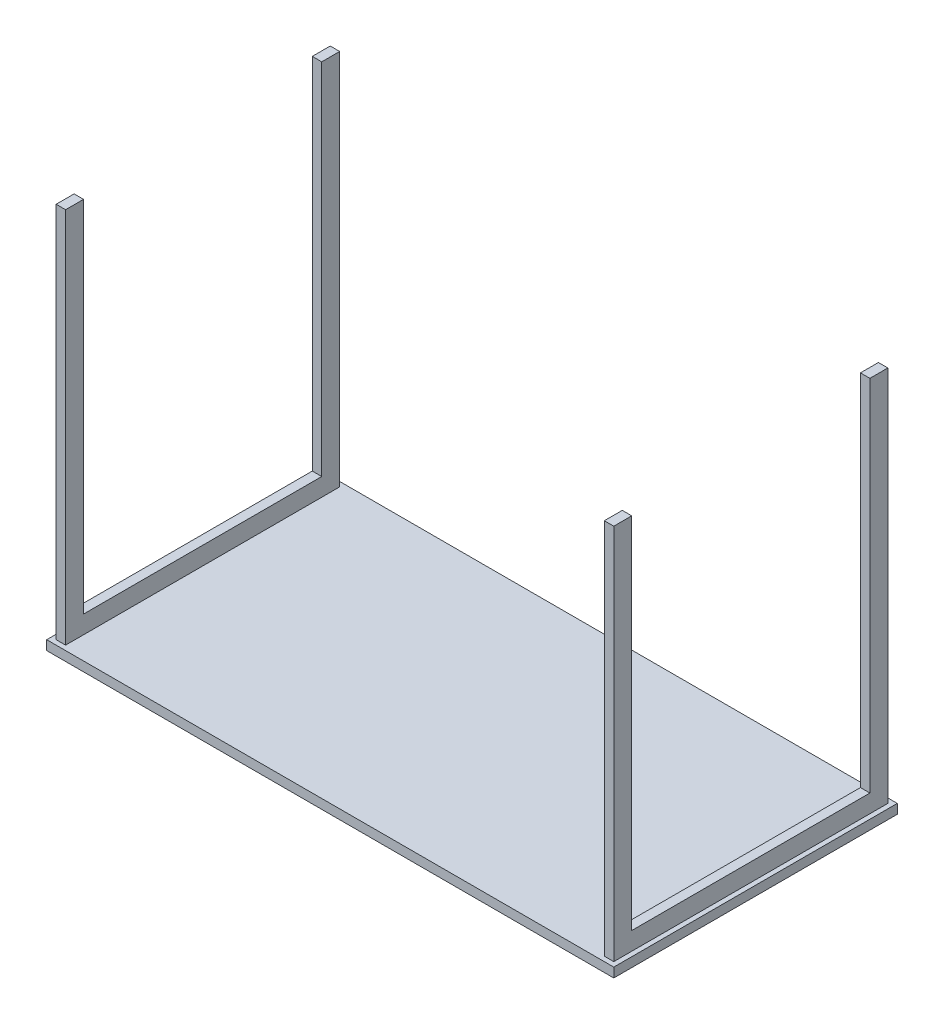
SolidWorks part; units mm, degrees
ref_plane "Front Plane" through (0, 0, 0) normal (0, 0, 1) x (1, 0, 0)
ref_plane "Top Plane" through (0, 0, 0) normal (0, 1, 0) x (1, 0, 0)
ref_plane "Right Plane" through (0, 0, 0) normal (1, 0, 0) x (0, 0, -1)
sketch "Sketch9" plane through (0, 0, 0) normal (0, 1, 0) x (1, 0, 0)
  line L0 (0, 0) -> (0, 600)
  line L1 (0, 0) -> (1200, 0)
  line L2 (0, 600) -> (1200, 600)
  line L3 (1200, 0) -> (1200, 600)
extrude "Boss-Extrude4" add sketch "Sketch9" along normal blind 20
sketch "Sketch10" plane through (0, 20, 0) normal (0, 1, 0) x (1, 0, 0)
  line L0 (10, 590) -> (10, 10)
  line L1 (10, 590) -> (30, 590)
  line L2 (10, 10) -> (30, 10)
  line L3 (30, 590) -> (30, 10)
  line L4 (0, 600) -> (0, 0) construction
  line L6 (1200, 600) -> (0, 600) construction
  line L7 (600, 600) -> (600, 0) construction
  line L8 (0, 0) -> (1200, 0) construction
  line L9 (1170, 590) -> (1170, 10)
  line L10 (1190, 10) -> (1170, 10)
  line L11 (1190, 590) -> (1170, 590)
  line L12 (1190, 590) -> (1190, 10)
  dimension "D1" = 10
  dimension "D2" = 20
  dimension "D3" = 10
  dimension "D4" = 10
extrude "Boss-Extrude6" add sketch "Sketch10" along normal blind 38
sketch "Sketch11" plane through (0, 58, 0) normal (0, 1, 0) x (1, 0, 0)
  line L0 (10, 590) -> (10, 552)
  line L1 (10, 590) -> (30, 590)
  line L2 (10, 552) -> (30, 552)
  line L3 (30, 590) -> (30, 552)
  line L4 (10, 590) -> (10, 10) construction
  line L5 (30, 10) -> (30, 590) construction
  line L6 (10, 300) -> (1190, 300) construction
  line L7 (1190, 10) -> (1190, 590) construction
  line L8 (600, 600) -> (600, 0) construction
  line L9 (1200, 600) -> (0, 600) construction
  line L10 (0, 0) -> (1200, 0) construction
  line L11 (30, 10) -> (30, 48)
  line L12 (10, 48) -> (30, 48)
  line L13 (10, 10) -> (30, 10)
  line L14 (10, 10) -> (10, 48)
  line L15 (1190, 10) -> (1190, 48)
  line L16 (1190, 10) -> (1170, 10)
  line L17 (1190, 48) -> (1170, 48)
  line L18 (1170, 10) -> (1170, 48)
  line L19 (1170, 590) -> (1170, 552)
  line L20 (1190, 552) -> (1170, 552)
  line L21 (1190, 590) -> (1170, 590)
  line L22 (1190, 590) -> (1190, 552)
  dimension "D1" = 38
extrude "Boss-Extrude7" add sketch "Sketch11" along normal blind 760
